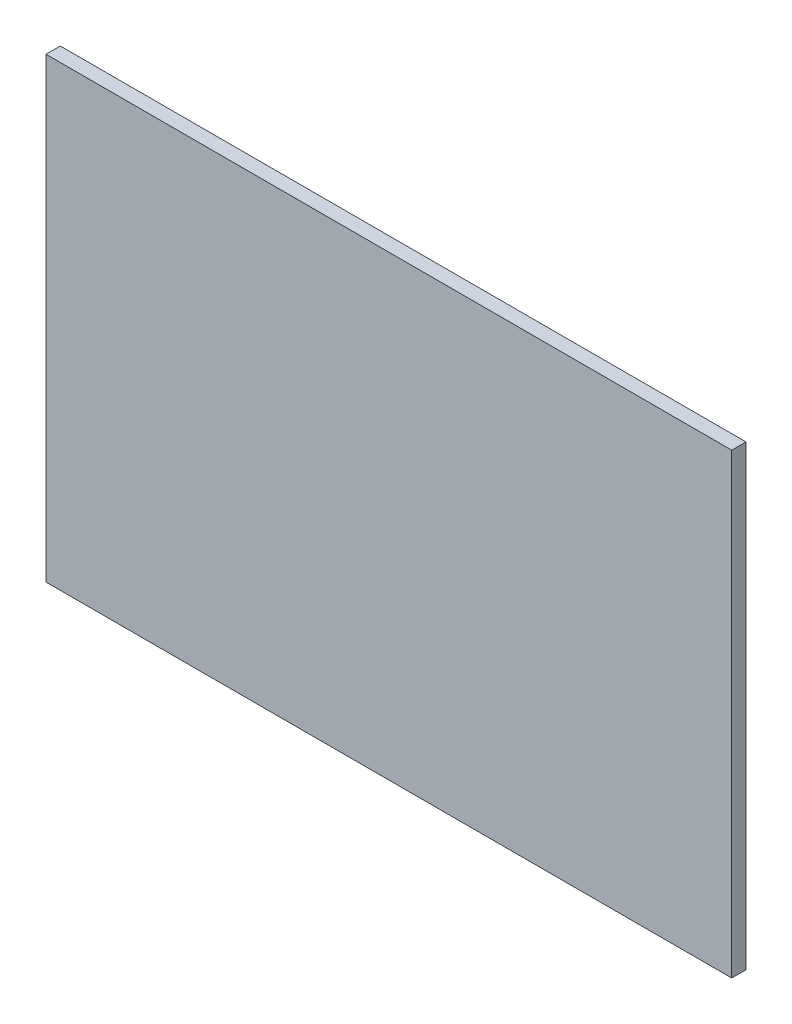
SolidWorks part; units mm, degrees
ref_plane "Front Plane" through (0, 0, 0) normal (0, 0, 1) x (1, 0, 0)
ref_plane "Top Plane" through (0, 0, 0) normal (0, 1, 0) x (1, 0, 0)
ref_plane "Right Plane" through (0, 0, 0) normal (1, 0, 0) x (0, 0, -1)
sketch "Sketch1" plane through (0, 0, 0) normal (0, 0, 1) x (1, 0, 0)
  line L1 (0, 0) -> (304.8, 0)
  line L2 (0, 0) -> (0, 203.2)
  line L3 (0, 203.2) -> (304.8, 203.2)
  line L4 (304.8, 0) -> (304.8, 203.2)
  dimension "D1" = 203.2
  dimension "D2" = 304.8
extrude "Boss-Extrude1" add sketch "Sketch1" along normal blind 6.35
